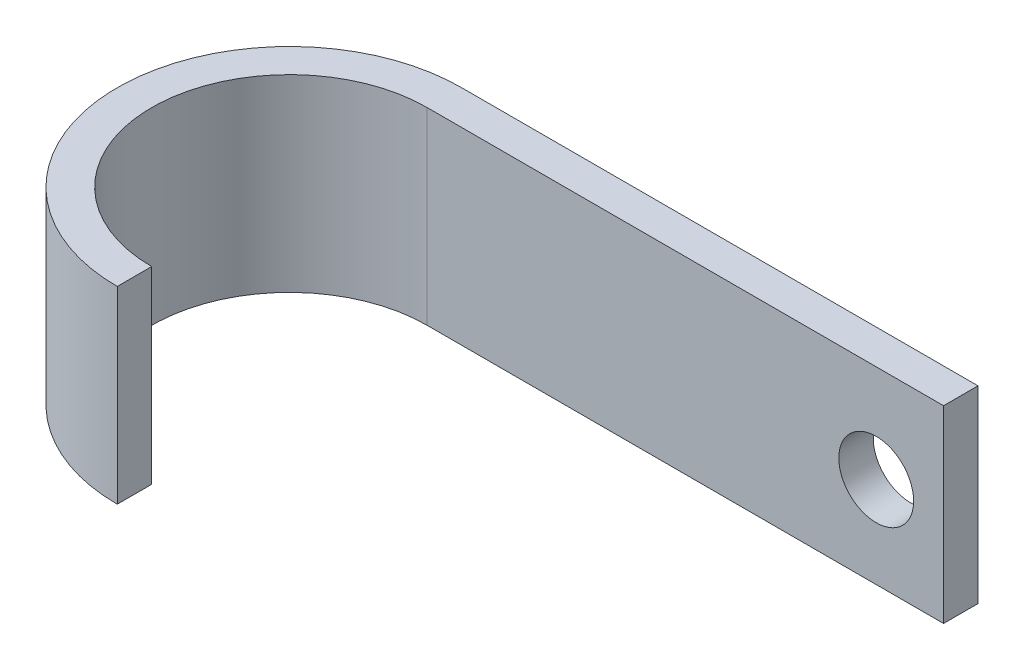
SolidWorks part; units mm, degrees
ref_plane "Front Plane" through (0, 0, 0) normal (0, 0, 1) x (1, 0, 0)
ref_plane "Top Plane" through (0, 0, 0) normal (0, 1, 0) x (1, 0, 0)
ref_plane "Right Plane" through (0, 0, 0) normal (1, 0, 0) x (0, 0, -1)
sketch "Sketch1" plane through (0, 0, 0) normal (0, 1, 0) x (1, 0, 0)
  line L0 (0, 11.5) -> (11.5, 11.5)
  line L1 (11.5, 11.5) -> (11.5, 0) construction
  line L2 (11.5, 11.5) -> (34.5, 11.5)
  line L3 (34.5, 11.5) -> (34.5, 9.2)
  line L4 (34.5, 9.2) -> (0, 9.2)
  line L5 (0, -11.5) -> (0, -9.2)
  circle A0 centre (0, 0) radius 11.5 construction
  arc A1 (0, 11.5) -> (0, -11.5) centre (0, 0) ccw
  arc A2 (0, -9.2) -> (0, 9.2) centre (0, 0) cw
  point P12 (0.2348, 10.8264)
  dimension "D3" = 11.5
  dimension "D1" = 2.3
  dimension "D2" = 2.3
  dimension "D4" = 23
extrude "Boss-Extrude1" add sketch "Sketch1" along normal blind 12.6
sketch "Sketch2" plane through (0, 0, -9.2) normal (0, 0, 1) x (1, 0, 0)
  line L0 (34.5, 12.6) -> (34.5, 0) construction
  circle A0 centre (30, 6.08) radius 2.5
  dimension "D2" = 5
  dimension "D1" = 4.5
extrude "Cut-Extrude1" cut sketch "Sketch2" against normal blind 12.6
